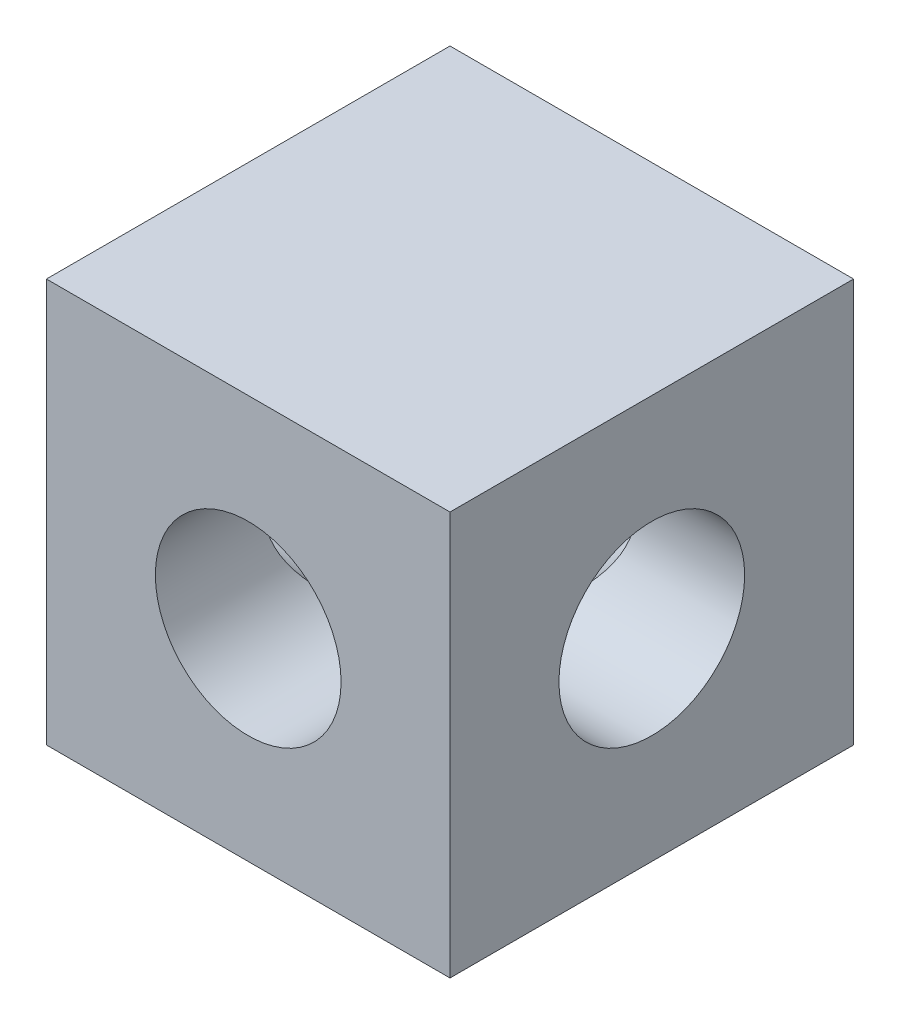
SolidWorks part; units mm, degrees
ref_plane "Front Plane" through (0, 0, 0) normal (0, 0, 1) x (1, 0, 0)
ref_plane "Top Plane" through (0, 0, 0) normal (0, 1, 0) x (1, 0, 0)
ref_plane "Right Plane" through (0, 0, 0) normal (1, 0, 0) x (0, 0, -1)
sketch "Sketch1" plane through (0, 0, 0) normal (0, 1, 0) x (1, 0, 0)
  line L1 (10.16, 10.16) -> (-10.16, 10.16)
  line L2 (10.16, 10.16) -> (10.16, -10.16)
  line L3 (10.16, -10.16) -> (-10.16, -10.16)
  line L4 (-10.16, 10.16) -> (-10.16, -10.16)
  line L5 (10.16, 10.16) -> (-10.16, -10.16) construction
  line L6 (10.16, -10.16) -> (-10.16, 10.16) construction
  point P0 (0, 0)
  dimension "D1" = 20.32
  dimension "D2" = 20.32
extrude "Boss-Extrude1" add sketch "Sketch1" along normal blind 20.32
sketch "Sketch2" plane through (0, 0, 10.16) normal (0, 0, 1) x (1, 0, 0)
  line L0 (0, 20.32) -> (0, 0) construction
  line L1 (-10.16, 20.32) -> (10.16, 20.32) construction
  circle A0 centre (0, 10.16) radius 4.675
  dimension "D1" = 9.35
extrude "Cut-Extrude1" cut sketch "Sketch2" against normal blind 10.1 contours A0
sketch "Sketch3" plane through (0, 0, 0) normal (0, 0, 1) x (1, 0, 0)
  line L0 (0, 20.32) -> (0, 0) construction
  line L1 (-10.16, 20.32) -> (10.16, 20.32) construction
pattern_circular "CirPattern1" count 4 over 360 about axis through (0, 0, 0) along (0, 1, 0) of "Cut-Extrude1"
